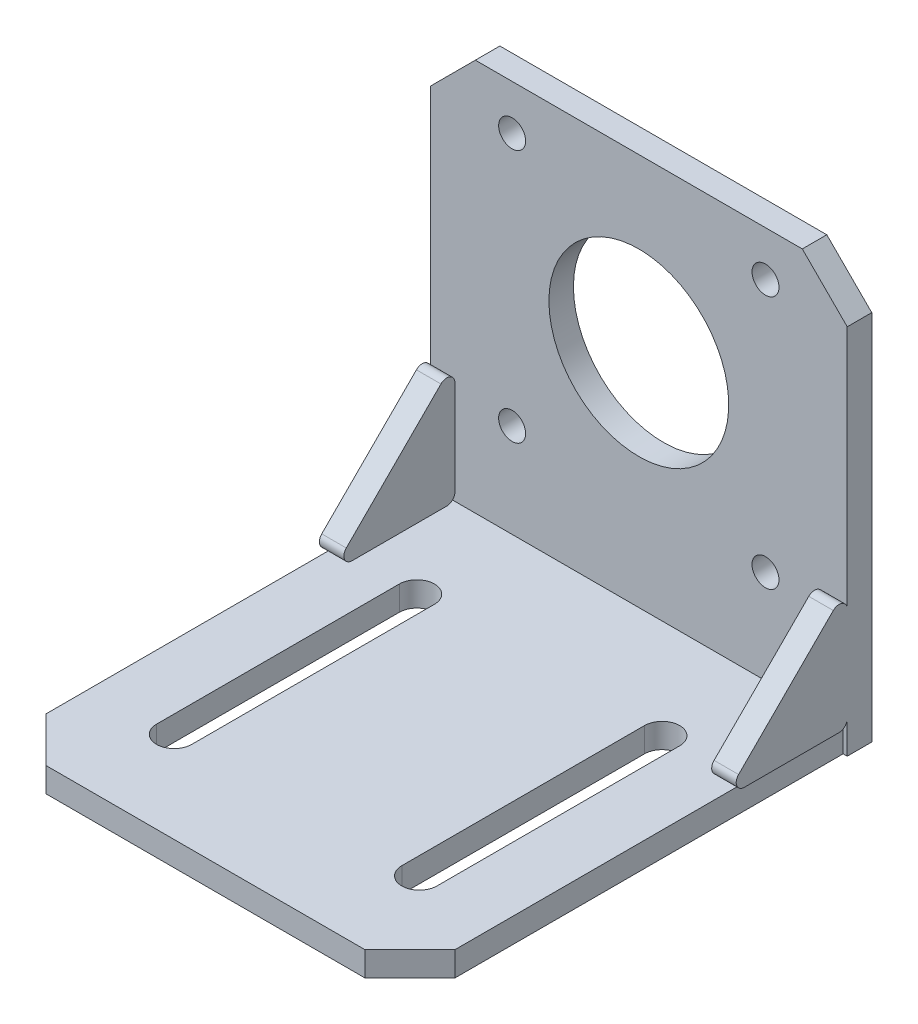
SolidWorks part; units mm, degrees
ref_plane "前视基准面" through (0, 0, 0) normal (0, 0, 1) x (1, 0, 0)
ref_plane "上视基准面" through (0, 0, 0) normal (0, 1, 0) x (1, 0, 0)
ref_plane "右视基准面" through (0, 0, 0) normal (1, 0, 0) x (0, 0, -1)
sketch "草图1" plane through (0, 0, 0) normal (0, 1, 0) x (1, 0, 0)
  line L0 (19.5, -53) -> (25, -47.5)
  line L1 (-25, 0) -> (25, 0)
  line L2 (-25, 0) -> (-25, -47.5)
  line L3 (-19.5, -53) -> (19.5, -53)
  line L4 (25, 0) -> (25, -47.5)
  line L5 (-25, -47.5) -> (-19.5, -53)
  line L6 (15, -12.15) -> (15, -41.85) construction
  line L7 (17.15, -12.15) -> (17.15, -41.85)
  line L8 (12.85, -12.15) -> (12.85, -41.85)
  line L9 (0, 0) -> (0, -32.7927) construction
  line L10 (-15, -12.15) -> (-15, -41.85) construction
  line L11 (-17.15, -12.15) -> (-17.15, -41.85)
  line L12 (-12.85, -12.15) -> (-12.85, -41.85)
  arc A0 (17.15, -12.15) -> (12.85, -12.15) centre (15, -12.15) ccw
  arc A1 (12.85, -41.85) -> (17.15, -41.85) centre (15, -41.85) ccw
  arc A2 (-17.15, -12.15) -> (-12.85, -12.15) centre (-15, -12.15) cw
  arc A3 (-12.85, -41.85) -> (-17.15, -41.85) centre (-15, -41.85) cw
  point P1 (25, -53)
  point P2 (-25, -53)
  point P11 (15, -27)
  point P16 (15, -10)
  point P17 (15, -44)
  point P22 (-15, -27)
  dimension "D1" = 53
  dimension "D2" = 50
  dimension "D3" = 34
  dimension "D4" = 9
  dimension "D7" = 7.85
  dimension "D8" = 4.3
extrude "凸台-拉伸1" add sketch "草图1" against normal blind 3
sketch "草图2" plane through (0, 0, 0) normal (0, 0, -1) x (-1, 0, 0)
  line L0 (-25, 0) -> (25, 0) construction
  line L1 (-25.5, -3) -> (25.5, -3)
  line L2 (-25.5, -3) -> (-25.5, 42.5)
  line L3 (-20, 48) -> (20, 48)
  line L4 (25.5, -3) -> (25.5, 42.5)
  line L5 (0, 27) -> (11, 27) construction
  line L6 (0, 27) -> (0, 38) construction
  line L7 (20, 48) -> (25.5, 42.5)
  line L8 (-25.5, 42.5) -> (-20, 48)
  circle A0 centre (0, 27) radius 11
  circle A1 centre (-15.5, 42.5) radius 1.65
  circle A2 centre (-15.5, 11.5) radius 1.65
  circle A3 centre (15.5, 11.5) radius 1.65
  circle A4 centre (15.5, 42.5) radius 1.65
  point P1 (25.5, 48)
  point P2 (-25.5, 48)
  point P6 (0, -3)
  dimension "D4" = 3.3
  dimension "D5" = 31
  dimension "D6" = 31
  dimension "D7" = 21
  dimension "D8" = 22
  dimension "D1" = 51
  dimension "D2" = 51
  dimension "D3" = 3
extrude "凸台-拉伸2" add sketch "草图2" along normal blind 3
ref_plane "基准面1" through (25, 0, 0) normal (0, 0, -1) x (-1, 0, 0)
sketch "草图4" plane through (25.5, 0, 0) normal (1, 0, 0) x (0, 0, -1)
  line L0 (-1.7071, 13.2929) -> (-13.2929, 1.7071)
  line L1 (0, 42.5) -> (0, -3) construction
  line L2 (-47.5, 0) -> (0, 0) construction
  line L3 (0, 12.5858) -> (0, 1)
  line L4 (-1, 0) -> (-12.5858, 0)
  arc A0 (-13.2929, 1.7071) -> (-12.5858, 0) centre (-12.5858, 1) ccw
  arc A1 (0, 1) -> (-1, 0) centre (-1, 1) cw
  arc A2 (-1.7071, 13.2929) -> (0, 12.5858) centre (-1, 12.5858) cw
  point P10 (-15, 0)
  point P13 (0, 0)
  point P16 (0, 15)
  dimension "D3" = 1
  dimension "D1" = 15
  dimension "D2" = 15
extrude "凸台-拉伸3" add sketch "草图4" against normal blind 3
mirror "镜向1" about plane through (0, 0, 0) normal (1, 0, 0) of "凸台-拉伸3"
